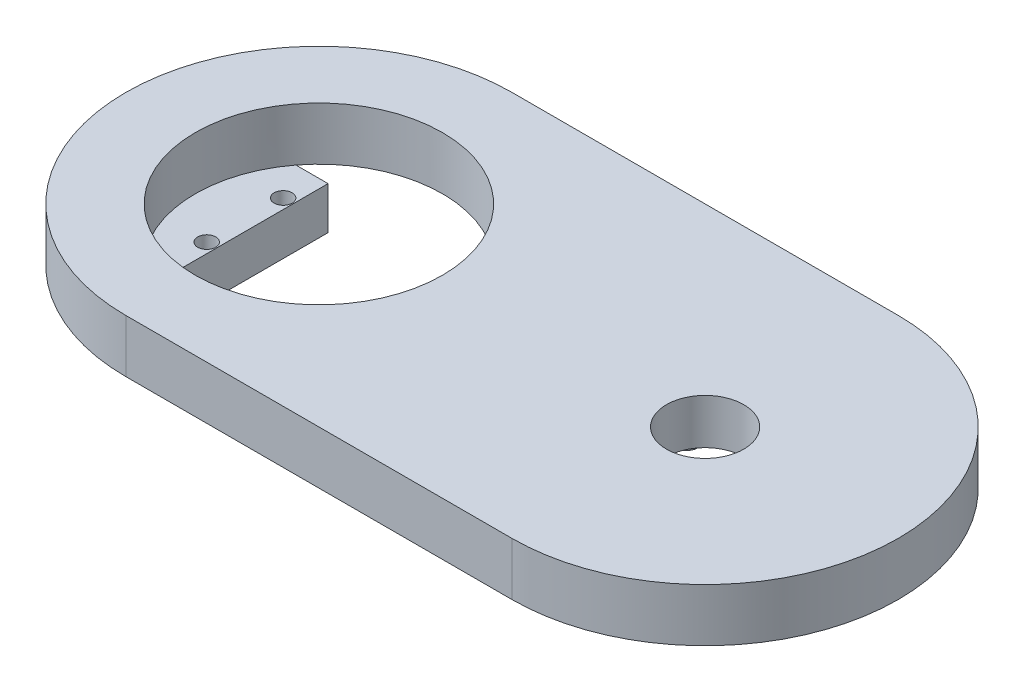
SolidWorks part; units mm, degrees
ref_plane "Front Plane" through (0, 0, 0) normal (0, 0, 1) x (1, 0, 0)
ref_plane "Top Plane" through (0, 0, 0) normal (0, 1, 0) x (1, 0, 0)
ref_plane "Right Plane" through (0, 0, 0) normal (1, 0, 0) x (0, 0, -1)
sketch "Sketch1" plane through (0, 0, 0) normal (0, 1, 0) x (1, 0, 0)
  line L0 (-13.2641, 0) -> (36.7359, 0) construction
  line L1 (-13.2641, 25) -> (36.7359, 25)
  line L2 (-13.2641, -25) -> (36.7359, -25)
  arc A0 (-13.2641, 25) -> (-13.2641, -25) centre (-13.2641, 0) ccw
  arc A1 (36.7359, -25) -> (36.7359, 25) centre (36.7359, 0) ccw
  point P3 (11.7359, 0)
  point P8 (61.7359, 0)
  point P9 (-38.2641, 0)
  point P10 (11.7359, 25)
  point P11 (11.7359, -25)
  dimension "D1" = 100
  dimension "D2" = 50
extrude "Boss-Extrude1" add sketch "Sketch1" along normal blind 6.86
sketch "Sketch2" plane through (0, 6.86, 0) normal (0, 1, 0) x (1, 0, 0)
  circle A0 centre (36.7359, 0) radius 5
  circle A1 centre (-13.2641, 0) radius 16
  arc A3 (-13.2641, 25) -> (-13.2641, -25) centre (-13.2641, 0) ccw construction
  arc A4 (36.7359, -25) -> (36.7359, 25) centre (36.7359, 0) ccw construction
  point P7 (-38.2641, 0)
  point P12 (61.7359, 0)
  dimension "D1" = 32
  dimension "D4" = 10
  dimension "D2" = 25
  dimension "D3" = 25
extrude "Cut-Extrude1" cut sketch "Sketch2" against normal blind 6.86
sketch "Sketch3" plane through (0, 0, 0) normal (0, -1, 0) x (1, 0, 0)
  line L0 (-33.3041, 9.2689) -> (-21.8041, 9.2689)
  line L5 (14.6959, 9.3588) -> (21.6959, 9.3588)
  line L6 (14.6959, 9.3588) -> (14.6959, -9.6412)
  line L7 (14.6959, -9.6412) -> (21.6959, -9.6412)
  line L8 (21.6959, 9.3588) -> (21.6959, -9.6412)
  line L13 (-33.3041, 9.2689) -> (-33.3041, -9.7311)
  line L14 (-33.3041, -9.7311) -> (-21.8041, -9.7311)
  line L15 (-21.8041, 9.2689) -> (-21.8041, -9.7311)
  circle A1 centre (-13.2641, 0) radius 16 construction
  point P4 (-33.3041, -0.2311)
  point P11 (-21.8041, -0.2311)
  point P12 (21.6959, -0.1412)
  dimension "D1" = 55
  dimension "D2" = 8.54
  dimension "D4" = 19
extrude "Boss-Extrude2" add sketch "Sketch3" along normal blind 5.5
sketch "Sketch4" plane through (0, -5.5, 0) normal (0, -1, 0) x (1, 0, 0)
  line L3 (-33.3041, 9.2689) -> (-33.3041, -9.7311) construction
  line L4 (-33.3041, -9.7311) -> (-21.8041, -9.7311) construction
  circle A2 centre (-23.1041, 4.6789) radius 1.165
  circle A3 centre (-23.1041, -5.2111) radius 1.165
  dimension "D5" = 10.2
  dimension "D6" = 10.2
  dimension "D7" = 4.52
  dimension "D8" = 9.89
extrude "Cut-Extrude2" cut sketch "Sketch4" against normal blind 12.5
sketch "Sketch6" plane through (0, 0, 0) normal (0, 1, 0) x (1, 0, 0)
  circle A0 centre (36.7359, 0) radius 12
extrude "Cut-Extrude3" cut sketch "Sketch6" along normal blind 1
sketch "Sketch7" plane through (0, 0, 0) normal (0, 1, 0) x (1, 0, 0)
  circle A0 centre (36.7359, -9) radius 1.5
  circle A1 centre (36.7359, 0) radius 5 construction
  circle A4 centre (29.268, 5.0592) radius 1.4937
  circle A5 centre (44.2438, 4.9658) radius 1.5
  dimension "D1" = 9.0016
  dimension "D4" = 15.856
  dimension "D5" = 14.9758
  dimension "D6" = 15.9195
  dimension "D2" = 9.0203
  dimension "D3" = 9
extrude "Boss-Extrude5" add sketch "Sketch7" against normal blind 1 and the other way blind 1
